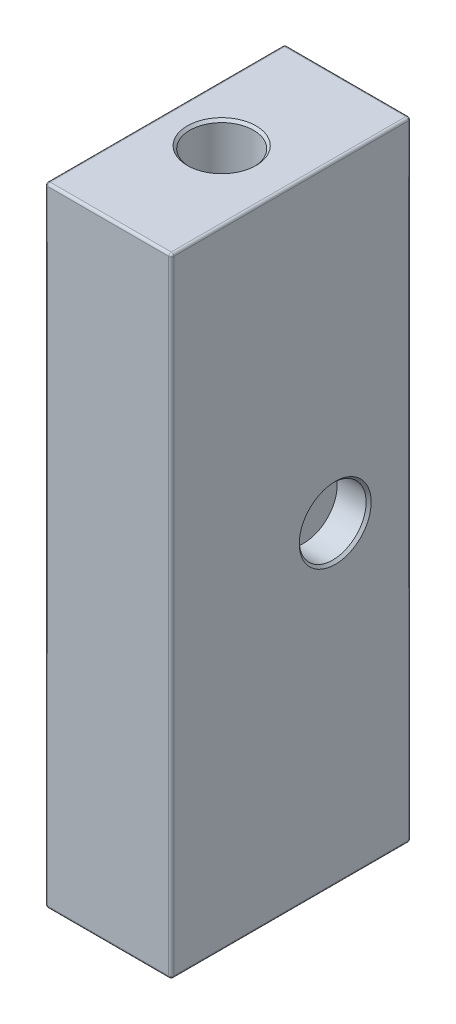
SolidWorks part; units mm, degrees
material "ABS"
ref_plane "Front Plane" through (0, 0, 0) normal (0, 0, 1) x (1, 0, 0)
ref_plane "Top Plane" through (0, 0, 0) normal (0, 1, 0) x (1, 0, 0)
ref_plane "Right Plane" through (0, 0, 0) normal (1, 0, 0) x (0, 0, -1)
sketch "Sketch1" plane through (0, 0, 0) normal (0, 1, 0) x (1, 0, 0)
  line L6 (5, -9.5) -> (-5, -9.5)
  line L9 (5, -9.5) -> (5, 9.5)
  line L10 (5, 9.5) -> (-5, 9.5)
  line L11 (-5, -9.5) -> (-5, 9.5)
  line L13 (5, -9.5) -> (-5, 9.5) construction
  line L14 (5, 9.5) -> (-5, -9.5) construction
  circle A3 centre (-0.5, 0) radius 2.525 construction
  circle A4 centre (-0.5, 0) radius 2.525
  point P0 (0, 0)
  dimension "D1" = 10
  dimension "D3" = 19
extrude "Boss-Extrude1" add sketch "Sketch1" along normal mid plane 49.8
sketch "Sketch2" plane through (5, 0, 0) normal (1, 0, 0) x (0, 0, -1)
  line L3 (-9.5, -25) -> (-9.5, 25) construction
  circle A0 centre (3.5, 0) radius 2.65
  dimension "D1" = 5.3
  dimension "D2" = 13
extrude "Cut-Extrude1" cut sketch "Sketch2" against normal blind 2.5
fillet "Fillet1" radius 0.2 12 edges at (5, 0, -9.5) (0, 24.9, -9.5) (0, -24.9, -9.5) (0, 24.9, 9.5) (5, 0, 9.5) (0, -24.9, 9.5) (-5, 0, -9.5) (-5, 24.9, 0) (-5, 0, 9.5) (-5, -24.9, 0) (5, 24.9, 0) (5, -24.9, 0)
chamfer "Chamfer1" distance 0.2 angle 45 2 edges at (5, 0, -6.15) (-0.5, 24.9, 2.525)
